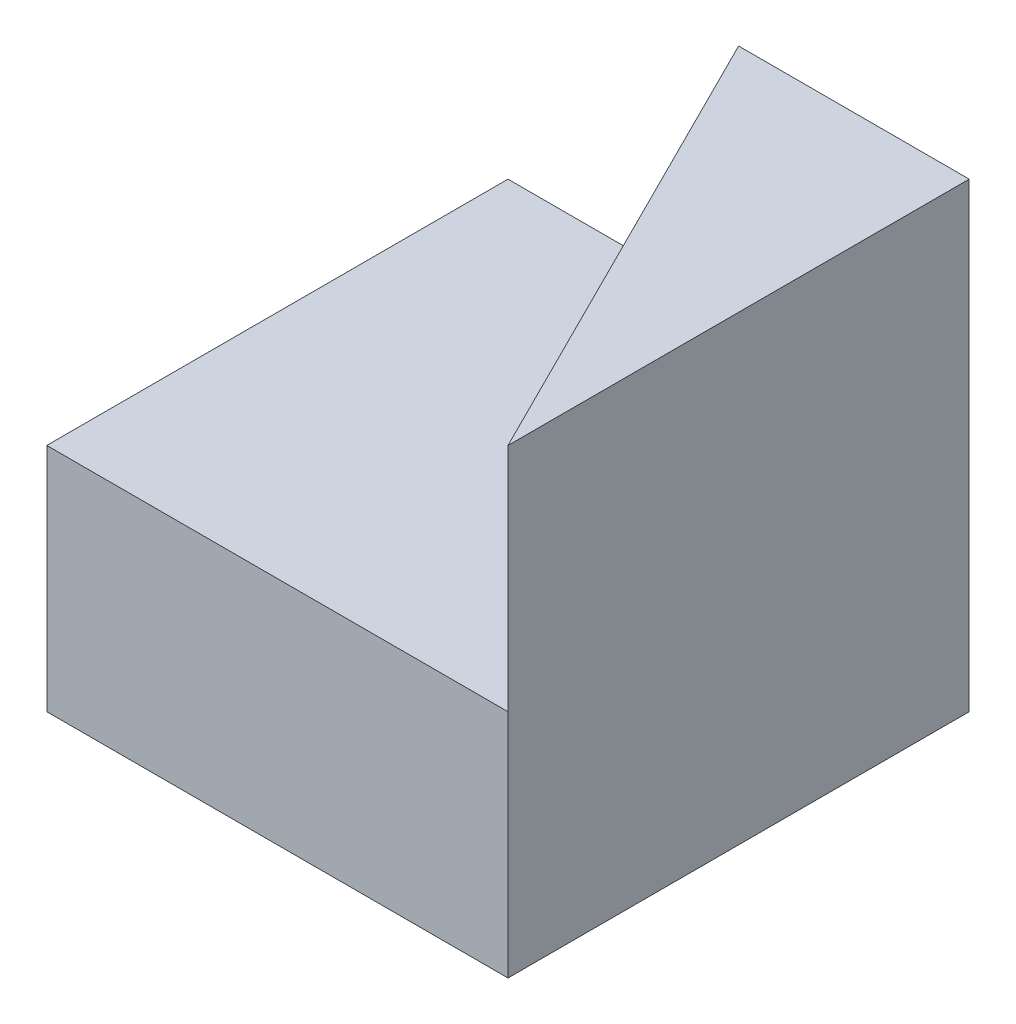
SolidWorks part; units mm, degrees
ref_plane "Front Plane" through (0, 0, 0) normal (0, 0, 1) x (1, 0, 0)
ref_plane "Top Plane" through (0, 0, 0) normal (0, 1, 0) x (1, 0, 0)
ref_plane "Right Plane" through (0, 0, 0) normal (1, 0, 0) x (0, 0, -1)
sketch "Sketch1" plane through (0, 0, 0) normal (0, 0, 1) x (1, 0, 0)
  line L1 (0, 0) -> (40, 0)
  line L2 (0, 0) -> (0, 20)
  line L3 (0, 20) -> (40, 20)
  line L4 (40, 0) -> (40, 20)
  dimension "D1" = 40
  dimension "D2" = 20
extrude "Boss-Extrude2" add sketch "Sketch1" along normal blind 40
sketch "Sketch2" plane through (0, 20, 0) normal (0, 1, 0) x (1, 0, 0)
  line L0 (0, -40) -> (20, 0)
  line L1 (40, 0) -> (0, 0) construction
  line L2 (20, 0) -> (0, 0)
  line L3 (0, 0) -> (0, -40)
extrude "Cut-Extrude1" cut sketch "Sketch2" against normal blind 40
sketch "Sketch3" plane through (0, 20, 0) normal (0, 1, 0) x (1, 0, 0)
  line L0 (40, -40) -> (40, 0)
  line L1 (40, 0) -> (20, -40)
  line L2 (40, -40) -> (0, -40) construction
  line L3 (20, -40) -> (40, -40)
extrude "Boss-Extrude3" add sketch "Sketch3" along normal blind 20
sketch "Sketch4" plane through (0, 20, 0) normal (0, 1, 0) x (1, 0, 0)
  line L0 (0, -40) -> (20, 0)
  line L1 (20, 0) -> (40, 0)
  line L2 (40, 0) -> (20, -40)
  line L3 (20, -40) -> (0, -40)
extrude "Boss-Extrude4" add sketch "Sketch4" along normal blind 20
sketch "Sketch5" plane through (0, 40, 0) normal (0, 1, 0) x (1, 0, 0)
  line L0 (40, 0) -> (20, -40)
  line L1 (0, -40) -> (40, -40) construction
  line L2 (20, -40) -> (40, -40)
  line L3 (40, -40) -> (40, 0)
extrude "Cut-Extrude2" cut sketch "Sketch5" against normal blind 20
sketch "Sketch6" plane through (0, 0, 40) normal (0, 0, 1) x (1, 0, 0)
  line L0 (0, 40) -> (0, 0) construction
  line L1 (20, 40) -> (0, 40)
  line L2 (20, 40) -> (20, 20)
  line L3 (20, 20) -> (0, 20)
  line L4 (0, 40) -> (0, 20)
extrude "Cut-Extrude3" cut sketch "Sketch6" against normal blind 109
sketch "Sketch7" plane through (0, 20, 0) normal (0, 1, 0) x (1, 0, 0)
  line L0 (0, -40) -> (20, 0)
  line L1 (20, 0) -> (0, 0)
  line L2 (0, 0) -> (0, -40)
  line L3 (0, -40) -> (-0.5038, -40.1659)
  line M3 (20, 0) -> (0, -40)
extrude "Boss-Extrude5" add sketch "Sketch7" against normal blind 20 contours L1 L2 M3
sketch "Sketch8" plane through (0, 20, 0) normal (0, 1, 0) x (1, 0, 0)
  line L0 (20, -40) -> (40, -40)
  line L1 (40, -40) -> (40, 0)
  line L2 (40, 0) -> (20, -40)
extrude "Boss-Extrude6" add sketch "Sketch8" along normal blind 20
sketch "Sketch9" plane through (0, 40, 0) normal (0, 1, 0) x (1, 0, 0)
  line L0 (40, 0) -> (20, -40)
  line L1 (20, -40) -> (20, 0)
  line L2 (20, 0) -> (40, 0)
  line L3 (20, 0) -> (40, -40)
  line L4 (40, -40) -> (20, -40)
  line L5 (40, -40) -> (20, -40)
  line M1 (20, 0) -> (20, -40)
  line M2 (20, -40) -> (40, -40)
extrude "Cut-Extrude5" cut sketch "Sketch9" against normal blind 20 contours L3 L0 M1 | L3 L0 M2
